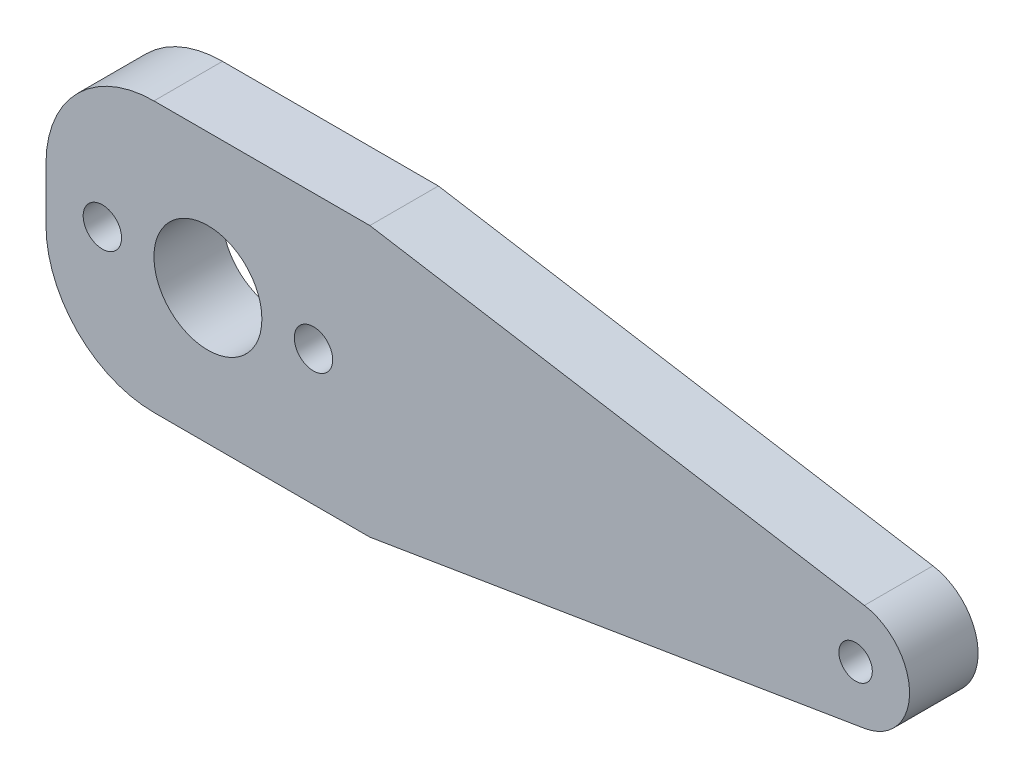
SolidWorks part; units mm, degrees
ref_plane "Front Plane" through (0, 0, 0) normal (0, 0, 1) x (1, 0, 0)
ref_plane "Top Plane" through (0, 0, 0) normal (0, 1, 0) x (1, 0, 0)
ref_plane "Right Plane" through (0, 0, 0) normal (1, 0, 0) x (0, 0, -1)
sketch "Sketch1" plane through (0, 0, 0) normal (0, 0, 1) x (1, 0, 0)
  line L0 (30, 25) -> (75.8148, 17.4331)
  line L1 (0, 0) -> (30, 0)
  line L2 (0, 0) -> (0, 25)
  line L3 (0, 25) -> (30, 25)
  line L5 (30, 0) -> (75.8148, 7.5668)
  circle A0 centre (15, 12.4999) radius 9.779
  circle A1 centre (75, 12.4999) radius 1.55
  circle A2 centre (5.221, 12.4999) radius 1.778
  circle A3 centre (24.779, 12.4999) radius 1.778
  circle A4 centre (75, 12.4999) radius 5
  circle A5 centre (15, 12.4999) radius 5
  dimension "D3" = 19.558
  dimension "D4" = 3.556
  dimension "D5" = 3.556
  dimension "D7" = 10
  dimension "D2" = 3.1
  dimension "D9" = 10
  dimension "D1" = 25
  dimension "D6" = 60
  dimension "D8" = 15
extrude "Boss-Extrude1" add sketch "Sketch1" along normal blind 6.35
fillet "Fillet1" radius 10 2 edges at (0, 0, 3.175) (0, 25, 3.175)
